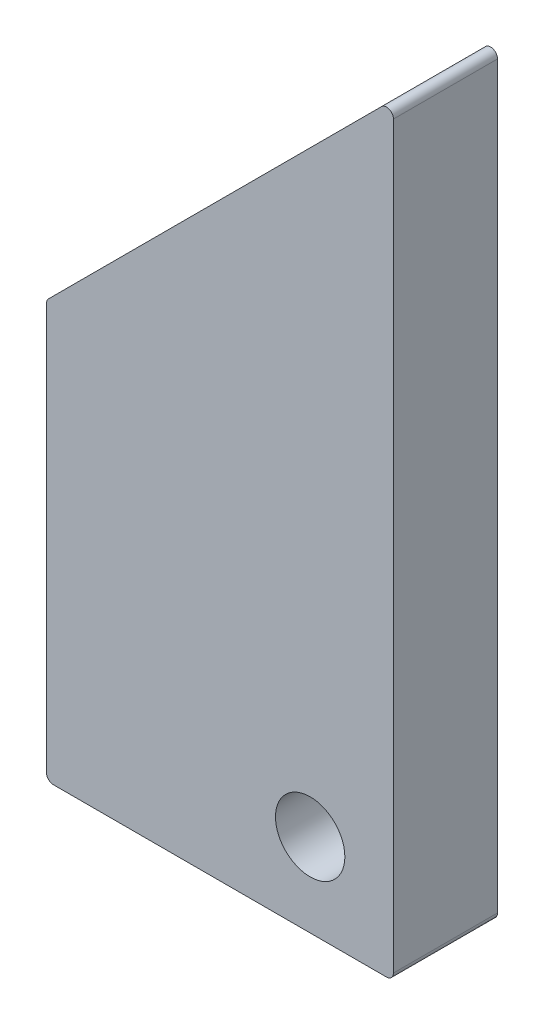
SolidWorks part; units mm, degrees
ref_plane "Piano frontale" through (0, 0, 0) normal (0, 0, 1) x (1, 0, 0)
ref_plane "Piano superiore" through (0, 0, 0) normal (0, 1, 0) x (1, 0, 0)
ref_plane "Piano destro" through (0, 0, 0) normal (1, 0, 0) x (0, 0, -1)
sketch "Schizzo1" plane through (0, 0, 0) normal (0, 0, 1) x (1, 0, 0)
  line L0 (0, 0) -> (0, 110)
  line L1 (0, 110) -> (-50, 60)
  line L2 (-50, 60) -> (-50, 0)
  line L3 (-50, 0) -> (0, 0)
  circle A0 centre (-12, 12) radius 5
  dimension "D4" = 10
  dimension "D5" = 12
  dimension "D6" = 12
  dimension "D1" = 110
  dimension "D2" = 50
  dimension "D3" = 60
extrude "Estrusione-Estrusione1" add sketch "Schizzo1" along normal blind 15
fillet "Raccordo1" radius 1 4 edges at (-50, 0, 7.5) (-50, 60, 7.5) (0, 0, 7.5) (0, 110, 7.5)
